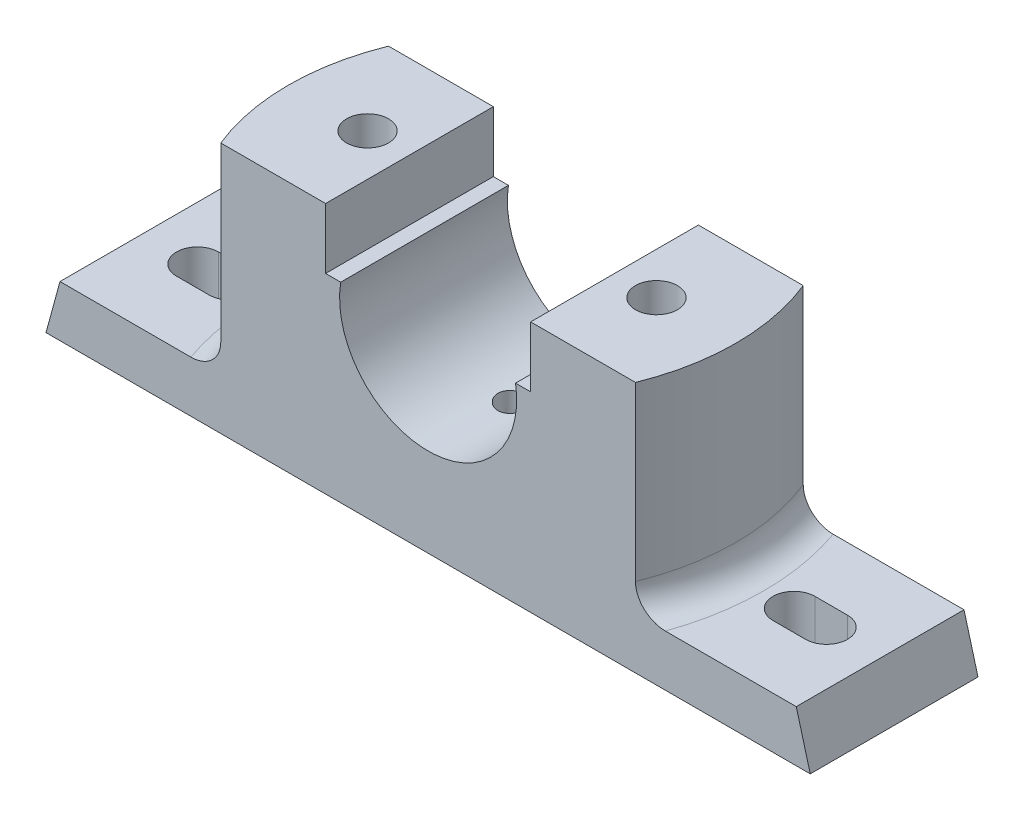
SolidWorks part; units mm, degrees
ref_plane "Front Plane" through (0, 0, 0) normal (0, 0, 1) x (1, 0, 0)
ref_plane "Top Plane" through (0, 0, 0) normal (0, 1, 0) x (1, 0, 0)
ref_plane "Right Plane" through (0, 0, 0) normal (1, 0, 0) x (0, 0, -1)
sketch "Sketch1" plane through (0, 0, 0) normal (0, 0, 1) x (1, 0, 0)
  line L0 (0, 0) -> (0, 90.1408) construction
  line L1 (-82, 0) -> (82, 0)
  line L2 (82, 0) -> (79, 11)
  line L3 (79, 11) -> (50, 11)
  line L4 (50, 11) -> (50, 54)
  line L5 (50, 54) -> (22, 54)
  line L6 (22, 54) -> (22, 41)
  line L7 (22, 41) -> (18.7617, 41)
  line L8 (-22, 41) -> (-18.7617, 41)
  line L9 (-22, 54) -> (-22, 41)
  line L10 (-50, 54) -> (-22, 54)
  line L11 (-50, 11) -> (-50, 54)
  line L12 (-79, 11) -> (-50, 11)
  line L13 (-82, 0) -> (-79, 11)
  arc A0 (-18.7617, 41) -> (18.7617, 41) centre (0, 38) ccw
  dimension "D7" = 19
  dimension "D1" = 164
  dimension "D2" = 3
  dimension "D3" = 54
  dimension "D4" = 11
  dimension "D5" = 13
  dimension "D6" = 16
  dimension "D8" = 44
  dimension "D9" = 100
extrude "Boss-Extrude1" add sketch "Sketch1" along normal mid plane 36
sketch "Sketch2" plane through (0, 54, 0) normal (0, 1, 0) x (1, 0, 0)
  line L0 (-22, 18) -> (-50, 18) construction
  line L1 (-22, -18) -> (-50, -18) construction
  line L2 (-44.4972, 18) -> (-50, 18)
  line L3 (-50, 18) -> (-50, -18)
  line L4 (-50, -18) -> (-44.4972, -18)
  arc A0 (-44.4972, 18) -> (-44.4972, -18) centre (0, 0) ccw
  line M2 (-22, 18) -> (-50, 18)
  line M3 (-50, 18) -> (-50, -18)
  line M4 (-50, -18) -> (-22, -18)
  dimension "D1" = 48
extrude "Cut-Extrude1" cut sketch "Sketch2" against normal blind 43 contours A0 M2 M3 | A0 L3 M4
mirror "Mirror1" about plane through (0, 0, 0) normal (1, 0, 0) of "Boss-Extrude1"
sketch "Sketch3" plane through (0, 54, 0) normal (0, 1, 0) x (1, 0, 0)
  line L1 (50, 18) -> (22, 18) construction
  line L2 (50, -18) -> (22, -18) construction
  line L6 (44.4972, 18) -> (50, 18)
  line L7 (50, 18) -> (50, -18)
  line L8 (50, -18) -> (50, 18) construction
  line L9 (44.4972, -18) -> (50, -18)
  arc A1 (44.4972, 18) -> (44.4972, -18) centre (0, 0) cw
  dimension "D2" = 48
extrude "Cut-Extrude2" cut sketch "Sketch3" against normal up to surface (43 mm away) up to face at (64.5, 11, 0)
mirror "Mirror2" about plane through (0, 0, 0) normal (1, 0, 0) of "Cut-Extrude2"
sketch "Sketch4" plane through (0, 0, 0) normal (0, -1, 0) x (1, 0, 0)
  line L1 (-41, 10) -> (-21, 10)
  line L2 (-41, 10) -> (-41, -10)
  line L3 (-41, -10) -> (-21, -10)
  line L4 (-21, 10) -> (-21, -10)
  line L5 (-41, 10) -> (-21, -10) construction
  line L6 (-41, -10) -> (-21, 10) construction
  point P0 (-31, 0)
  dimension "D1" = 31
  dimension "D2" = 20
  dimension "D3" = 20
extrude "Cut-Extrude3" cut sketch "Sketch4" against normal blind 8
mirror "Mirror3" about plane through (0, 0, 0) normal (1, 0, 0) of "Cut-Extrude3"
fillet "Fillet1" radius 6 2 edges at (48, 11, 0) (-48, 11, 0)
hole_wizard "Ø6.0mm Dowel Hole2" positions "Sketch11" profile "Sketch10" hole size "Ø6.0" standard "ANSI Metric"
sketch "Sketch11" plane through (0, 54, 0) normal (0, 1, 0) x (1, 0, 0)
  point P0 (-31, 0)
  dimension "D1" = 31
sketch "Sketch10" plane through (-31, 54, 0) normal (1, 0, 0) x (0, 0, 1)
  line L0 (0, 0) -> (0, 56.7039)
  line L1 (0, 56.7039) -> (4.5, 54)
  line L2 (4.5, 54) -> (4.5, 0)
  line L5 (4.5, 0) -> (0, 0)
  line L10 (0, 56.7039) -> (-4.5, 54) construction
  line L11 (0, -6.35) -> (0, 107.95) construction
  dimension "Hole Dia." = 9
  dimension "Hole Depth" = 54
  dimension "Drill Angle" = 118
mirror "Mirror4" about plane through (0, 0, 0) normal (1, 0, 0) of "Ø6.0mm Dowel Hole2"
sketch "Sketch18" plane through (0, 11, 0) normal (0, 1, 0) x (1, 0, 0)
  line L0 (-67.5, 0) -> (-60.5, 0) construction
  line L1 (-67.5, 4.5) -> (-60.5, 4.5)
  line L2 (-67.5, -4.5) -> (-60.5, -4.5)
  arc A0 (-67.5, 4.5) -> (-67.5, -4.5) centre (-67.5, 0) ccw
  arc A1 (-60.5, -4.5) -> (-60.5, 4.5) centre (-60.5, 0) ccw
  point P2 (-64, 0)
  dimension "D1" = 16
  dimension "D2" = 64
extrude "Cut-Extrude4" cut sketch "Sketch18" against normal through all
mirror "Mirror5" about plane through (0, 0, 0) normal (1, 0, 0) of "Cut-Extrude4"
hole_wizard "Ø6.0mm Dowel Hole3" positions "3DSketch1" profile "Sketch21" hole size "Ø6.0" standard "ANSI Metric"
sketch3d "3DSketch1"
  point P0 (0, 19, 0)
  point P1 (-148.4665, 0, -78.9537)
  dimension "D1" = 0
sketch "Sketch21" plane through (0, 19, 0) normal (1, 0, 0) x (0, 0, 1)
  line L0 (0, 0) -> (0, 7.8026)
  line L1 (0, 7.8026) -> (3, 6)
  line L2 (3, 6) -> (3, 0)
  line L5 (3, 0) -> (0, 0)
  line L10 (0, 7.8026) -> (-3, 6) construction
  line L11 (0, -6.35) -> (0, 107.95) construction
  dimension "Hole Dia." = 6
  dimension "Hole Depth" = 6
  dimension "Drill Angle" = 118
